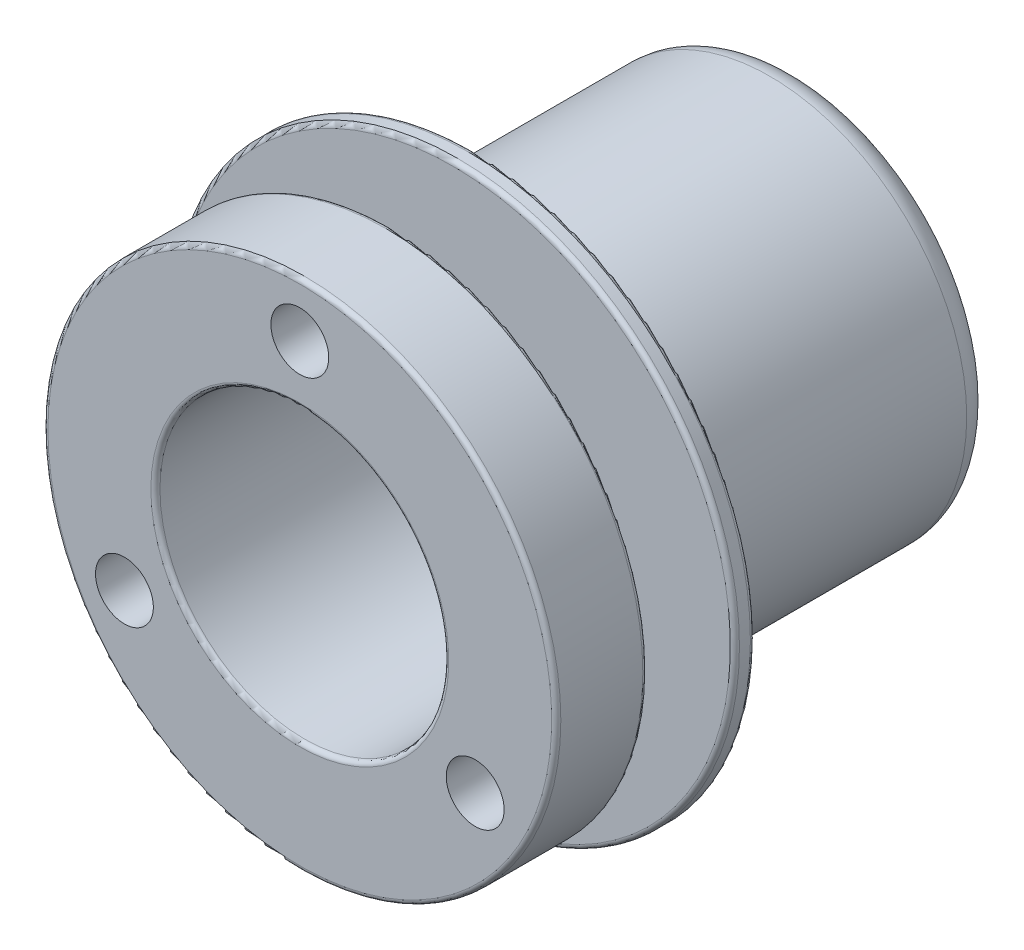
SolidWorks part; units mm, degrees
material "6061-T6 (SS)"
ref_plane "Front Plane" through (0, 0, 0) normal (0, 0, 1) x (1, 0, 0)
ref_plane "Top Plane" through (0, 0, 0) normal (0, 1, 0) x (1, 0, 0)
ref_plane "Right Plane" through (0, 0, 0) normal (1, 0, 0) x (0, 0, -1)
sketch "Sketch1" plane through (0, 0, 0) normal (1, 0, 0) x (0, 0, -1)
  line L0 (0, 15.85) -> (0, 28.15)
  line L1 (0, 28.15) -> (10, 28.15)
  line L2 (-9.8624, 0) -> (91.8242, 0) construction
  line L3 (10, 28.15) -> (10, 17.35)
  line L4 (10, 17.35) -> (16.8046, 17.35)
  line L5 (16.8046, 17.35) -> (16.8046, 30.95)
  line L6 (16.8046, 30.95) -> (19.0046, 30.95)
  line L7 (19.0046, 30.95) -> (19.0046, 21.6)
  line L8 (19.0046, 21.6) -> (51.6, 21.6)
  line L13 (54.6, 18.6) -> (54.6, 15.85)
  line L14 (54.6, 15.85) -> (0, 15.85)
  arc A0 (51.6, 21.6) -> (54.6, 18.6) centre (51.6, 18.6) cw
  dimension "D6" = 2.2
  dimension "D7" = 43.2
  dimension "D8" = 3
  dimension "D1" = 31.7
  dimension "D2" = 10
  dimension "D3" = 54.6
  dimension "D4" = 34.7
  dimension "D5" = 61.9
revolve "Revolve1" add sketch "Sketch1"
fillet "Fillet1" radius 0.5 5 edges at (15.85, 0, 0) (28.15, 0, 0) (28.15, 0, -10) (30.95, 0, -19.0046) (30.95, 0, -16.8046)
sketch "Sketch2" plane through (0, 0, 0) normal (0, 0, 1) x (1, 0, 0)
  line L0 (0, 0) -> (0, 33.1394) construction
  circle A0 centre (0, 0) radius 22.225 construction
  circle A1 centre (0, 22.225) radius 3.175
  circle A2 centre (19.2474, -11.1125) radius 3.175
  circle A3 centre (-19.2474, -11.1125) radius 3.175
  point P12 (0, 0)
  dimension "D1" = 6.35
  dimension "D2" = 44.45
  dimension "D3" = 3
extrude "Cut-Extrude1" cut sketch "Sketch2" against normal up to next
